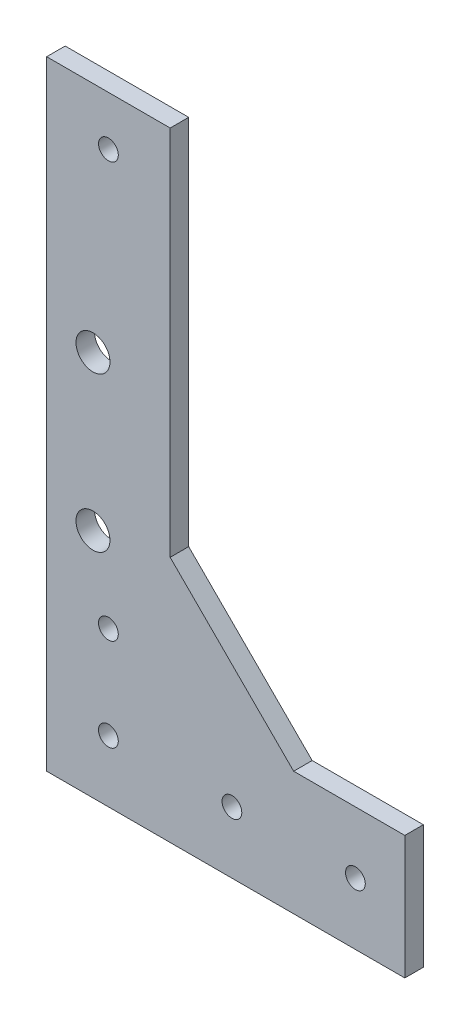
SolidWorks part; units mm, degrees
material "Thornel Mat VMA"
ref_plane "Front Plane" through (0, 0, 0) normal (0, 0, 1) x (1, 0, 0)
ref_plane "Top Plane" through (0, 0, 0) normal (0, 1, 0) x (1, 0, 0)
ref_plane "Right Plane" through (0, 0, 0) normal (1, 0, 0) x (0, 0, -1)
sketch "Sketch1" plane through (0, 0, 0) normal (0, 0, 1) x (1, 0, 0)
  line L0 (-195.4899, -7.503) -> (-195.4899, -27.503)
  line L1 (-233.4899, 12.497) -> (-213.4899, -7.503)
  line L2 (221.5101, -27.503) -> (-453.4899, -27.503) construction
  line L3 (-253.4899, 72.7096) -> (-253.4899, -27.503)
  line L4 (-253.4899, -7.503) -> (-253.4899, 282.497) construction
  line L5 (-253.4899, -27.503) -> (-195.4899, -27.503)
  line L6 (-253.4899, 72.7096) -> (-233.4899, 72.7096)
  line L7 (-233.4899, -7.503) -> (-233.4899, 282.497) construction
  line L8 (-233.4899, 72.7096) -> (-233.4899, 12.497)
  line L9 (-213.4899, -7.503) -> (-195.4899, -7.503)
  circle A0 centre (-243.4899, 64.7096) radius 1.6 construction
  circle A1 centre (-203.4899, -17.503) radius 1.6 construction
  point P14 (-233.4899, -7.503)
  dimension "D1" = 8
  dimension "D2" = 8
extrude "Extrude1" add sketch "Sketch1" along normal blind 3
sketch "Sketch2" plane through (0, 0, 3) normal (0, 0, 1) x (1, 0, 0)
  circle A0 centre (-203.4899, -17.503) radius 1.6 construction
  circle A1 centre (-223.4899, -17.503) radius 1.6 construction
  circle A2 centre (-243.4899, -17.503) radius 1.6 construction
  circle A3 centre (-243.4899, -2.503) radius 1.6 construction
  circle A4 centre (-245.9899, 9.9974) radius 2.75 construction
  circle A5 centre (-245.9899, 34.9974) radius 2.75 construction
  circle A6 centre (-243.4899, 64.7096) radius 1.6 construction
  circle A7 centre (-203.4899, -17.503) radius 1.6
  circle A8 centre (-223.4899, -17.503) radius 1.6
  circle A9 centre (-243.4899, -17.503) radius 1.6
  circle A10 centre (-243.4899, -2.503) radius 1.6
  circle A11 centre (-245.9899, 9.9974) radius 2.75
  circle A12 centre (-245.9899, 34.9974) radius 2.75
  circle A13 centre (-243.4899, 64.7096) radius 1.6
extrude "Cut-Extrude1" cut sketch "Sketch2" against normal blind 3
